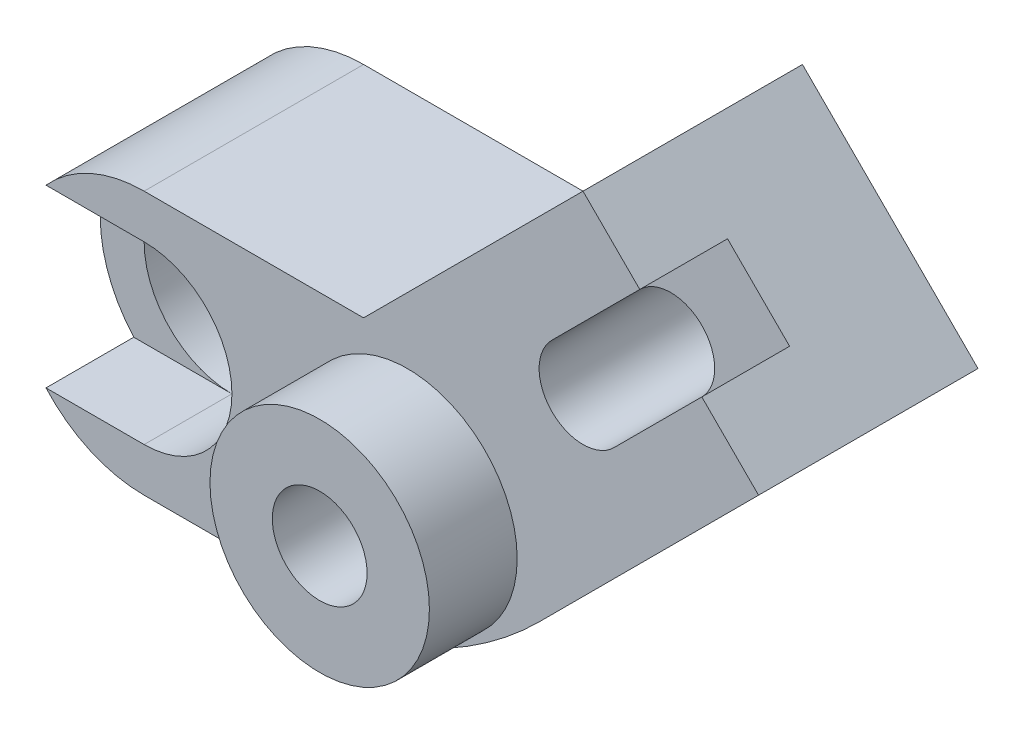
SolidWorks part; units mm, degrees
ref_plane "Front Plane" through (0, 0, 0) normal (0, 0, 1) x (1, 0, 0)
ref_plane "Top Plane" through (0, 0, 0) normal (0, 1, 0) x (1, 0, 0)
ref_plane "Right Plane" through (0, 0, 0) normal (1, 0, 0) x (0, 0, -1)
sketch "Sketch1" plane through (0, 0, 0) normal (0, 0, 1) x (1, 0, 0)
  line L0 (-45, -5) -> (-20, 20)
  line L1 (-20, 20) -> (0, 0)
  line L2 (-45, -5) -> (-70, -5)
  line L3 (-70, -35) -> (-40, -35)
  line L4 (0, 0) -> (-25, -25)
  arc A0 (-70, -5) -> (-70, -35) centre (-70, -20) ccw
  arc A1 (-40, -35) -> (-25, -25) centre (-57.5, 7.5) ccw
  dimension "D8" = 30
  dimension "D6" = 15
  dimension "D1" = 20
  dimension "D2" = 20
  dimension "D3" = 25
  dimension "D4" = 25
  dimension "D5" = 25
  dimension "D7" = 25
extrude "Boss-Extrude2" add sketch "Sketch1" along normal blind 25
sketch "Sketch2" plane through (0, 0, 25) normal (0, 0, 1) x (1, 0, 0)
  circle A0 centre (-20, 0) radius 5
  dimension "D1" = 10
  dimension "D2" = 25
  dimension "D3" = 5
extrude "Cut-Extrude1" cut sketch "Sketch2" against normal blind 63
sketch "Sketch3" plane through (0, 0, 25) normal (0, 0, 1) x (1, 0, 0)
  line L0 (-13.5351, 13.5351) -> (-23.5918, 3.4784)
  line L1 (-13.5351, 13.5351) -> (-6.4649, 6.4649)
  line L2 (0, 0) -> (-20, 20) construction
  line L5 (-6.4649, 6.4649) -> (-16.5216, -3.5918)
  line L6 (-25, -25) -> (0, 0) construction
  line L7 (-20, 20) -> (-45, -5) construction
  arc A0 (-23.5918, 3.4784) -> (-16.5216, -3.5918) centre (-20, 0) cw
  circle A1 centre (-20, 0) radius 5 construction
  point P12 (-20, 0)
  circle M1 centre (-20, 0) radius 5
  line M7 (0, 0) -> (-20, 20)
  dimension "D2" = 5
  dimension "D1" = 14.2224
extrude "Cut-Extrude2" cut sketch "Sketch3" against normal blind 10 contours L5 L0 M7 M1
sketch "Sketch4" plane through (0, 0, 25) normal (0, 0, 1) x (1, 0, 0)
  circle A0 centre (-40, -20) radius 12.5
  dimension "D1" = 25
  dimension "D2" = 15
extrude "Boss-Extrude4" add sketch "Sketch4" along normal blind 10
sketch "Sketch10" plane through (0, 0, 25) normal (0, 0, 1) x (1, 0, 0)
  circle A0 centre (-70, -20) radius 10
  dimension "D1" = 20
  dimension "D2" = 15
extrude "Cut-Extrude3" cut sketch "Sketch10" against normal blind 15
sketch "Sketch11" plane through (0, 0, 10) normal (0, 0, 1) x (1, 0, 0)
  circle A0 centre (-70, -20) radius 5
  point P3 (-70, -20)
  dimension "D1" = 10
extrude "Cut-Extrude4" cut sketch "Sketch11" against normal blind 872
sketch "Sketch12" plane through (0, 0, 25) normal (0, 0, 1) x (1, 0, 0)
  line L0 (-70, -30) -> (-81.1803, -30)
  line L1 (-70, -10) -> (-81.1803, -10)
  circle A0 centre (-70, -20) radius 10 construction
  arc A1 (-70, -5) -> (-70, -35) centre (-70, -20) ccw construction
  arc A2 (-70, -30) -> (-70, -10) centre (-70, -20) cw
  arc A3 (-81.1803, -30) -> (-81.1803, -10) centre (-70, -20) cw
  dimension "D3" = 15
  dimension "D1" = 11.1803
  dimension "D2" = 11.1803
extrude "Cut-Extrude6" cut sketch "Sketch12" against normal blind 10
hole_wizard "M12x1.25 Tapped Hole1" positions "Sketch13" profile "Sketch14" tap size "M12x1.25" standard "ISO"
sketch "Sketch13" plane through (0, 0, 35) normal (0, 0, 1) x (1, 0, 0)
  point P0 (-40, -20)
sketch "Sketch14" plane through (-40, -20, 35) normal (1, 0, 0) x (0, -1, 0)
  line L0 (0, 0) -> (0, 18.2446)
  line L1 (0, 18.2446) -> (5.4, 15)
  line L2 (5.4, 15) -> (5.4, 0)
  line L5 (5.4, 0) -> (0, 0)
  line L10 (0, 18.2446) -> (-5.4, 15) construction
  line L11 (0, -6.35) -> (0, 107.95) construction
  dimension "Tap Drill Dia." = 10.8
  dimension "Tap Drill Depth" = 15
  dimension "Drill Angle" = 118
cosmetic thread "Hole Thread1" parameters "D1"=15, "D2"=12
